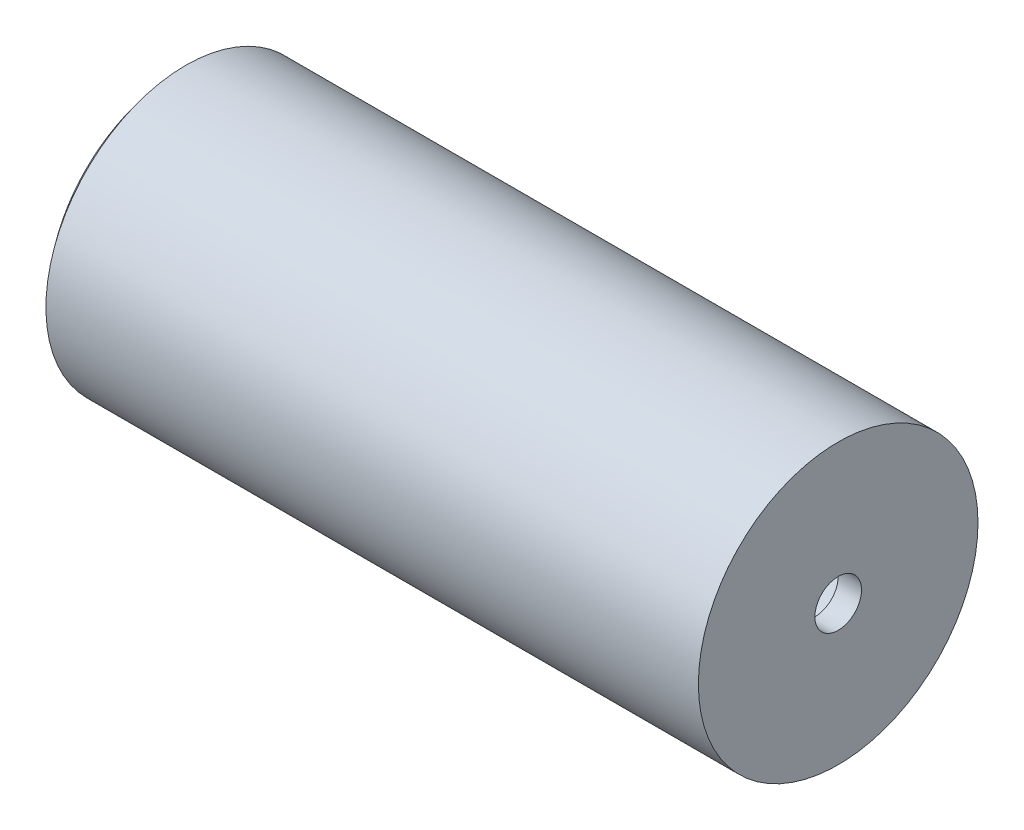
SolidWorks part; units mm, degrees
ref_plane "Спереди" through (0, 0, 0) normal (0, 0, 1) x (1, 0, 0)
ref_plane "Сверху" through (0, 0, 0) normal (0, 1, 0) x (1, 0, 0)
ref_plane "Справа" through (0, 0, 0) normal (1, 0, 0) x (0, 0, -1)
other "Configuration Table"
sketch "Sketch1" plane through (0, 0, 0) normal (0, 0, 1) x (1, 0, 0)
  line L0 (169.943, 5) -> (169.943, 30)
  line L1 (169.943, 30) -> (29.943, 30)
  line L3 (32.3576, 25) -> (164.943, 25)
  line L4 (164.943, 25) -> (164.943, 5)
  line L5 (164.943, 5) -> (169.943, 5)
  line L6 (0, 0) -> (-32.7693, 0) construction
  line L12 (19.0326, 0) -> (24.0326, 0)
  arc A2 (29.943, 30) -> (19.0326, 0) centre (65.7326, 0) ccw
  arc A3 (32.3576, 25) -> (24.0326, 0) centre (65.7326, 0) ccw
  point P12 (-77.6307, 0)
  point P13 (-41.4133, 30)
  point P14 (0, 0)
  point P15 (-49.2393, 30)
  point P16 (0, 0)
  point P17 (0, 0)
  point P18 (-16.3217, 30)
  point P19 (-26.0598, 25)
  point P20 (3.2176, 25)
  point P21 (5.3296, 25)
  point P22 (30.2367, 25)
  point P23 (4.943, 0)
  point P24 (0, 0)
  point P25 (4.943, 30)
  point P26 (6.6837, 0)
  point P27 (29.943, 30)
  point P28 (65.7326, 0)
  point P29 (0, 0)
  point P30 (23.9658, 0)
  dimension "D1" = 140
  dimension "D2" = 5
  dimension "D3" = 5
  dimension "D4" = 25
  dimension "D5" = 5
  dimension "D6" = 5
revolve "Revolve6" add sketch "Sketch1" angle 360 about L6
